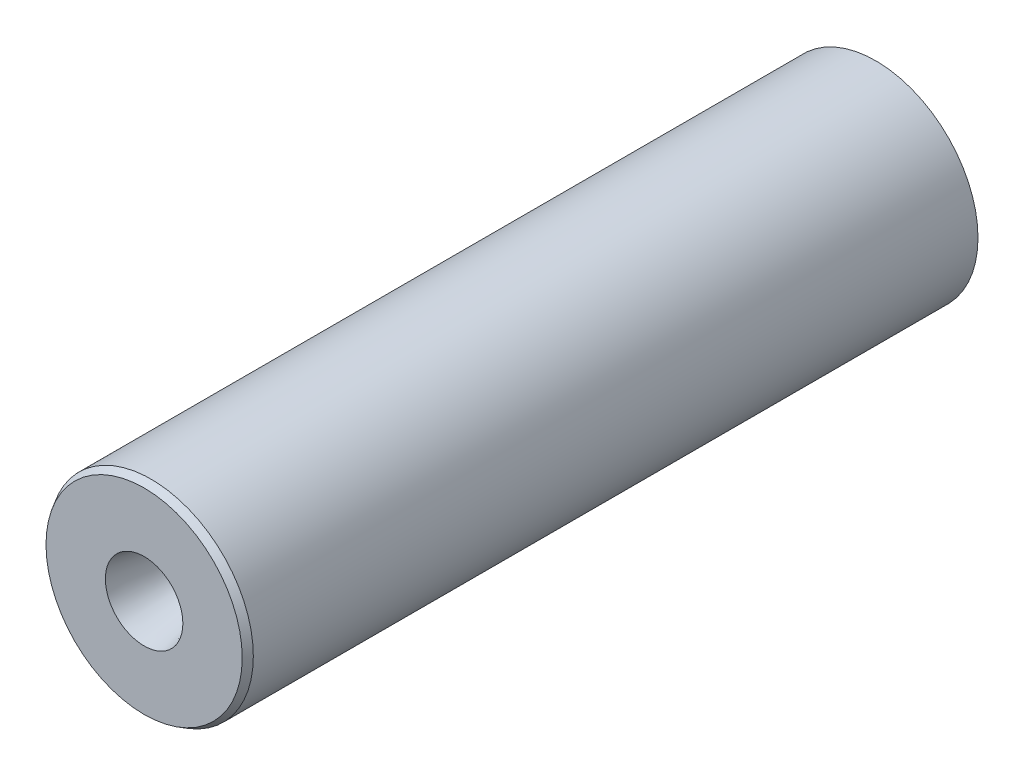
SolidWorks part; units mm, degrees
material "PLA"
ref_plane "Plan de face" through (0, 0, 0) normal (0, 0, 1) x (1, 0, 0)
ref_plane "Plan de dessus" through (0, 0, 0) normal (0, 1, 0) x (1, 0, 0)
ref_plane "Plan de droite" through (0, 0, 0) normal (1, 0, 0) x (0, 0, -1)
sketch "Esquisse1" plane through (0, 0, 0) normal (1, 0, 0) x (0, 0, -1)
  line L0 (-51.9182, 0) -> (51.9182, 0) construction
  line L1 (36.9182, 11) -> (36.9182, 9)
  line L2 (-51.9182, 14.5) -> (51.9182, 14.5)
  line L4 (-23.0818, 11) -> (36.9182, 11)
  line L6 (36.9182, 9) -> (51.9182, 9)
  line L7 (51.9182, 14.5) -> (51.9182, 9)
  line L8 (-23.0818, 11) -> (-37.8043, 2.5)
  line L9 (-37.8043, 2.5) -> (-51.9182, 5.5)
  line L10 (-51.9182, 14.5) -> (-51.9182, 5.5)
  line L11 (-47.6261, 7.6547) -> (-41.6462, 6.3836) construction
  line L12 (-47.4182, 11.5) -> (-33.9479, 11.5) construction
  line L13 (-48.4182, 10.5) -> (-48.4182, 8.6329) construction
  line L16 (-38.1066, 6.9443) -> (-33.4479, 9.634) construction
  arc A0 (-33.9479, 11.5) -> (-33.4479, 9.634) centre (-33.9479, 10.5) cw construction
  arc A1 (-48.4182, 8.6329) -> (-47.6261, 7.6547) centre (-47.4182, 8.6329) ccw construction
  arc A2 (-47.4182, 11.5) -> (-48.4182, 10.5) centre (-47.4182, 10.5) ccw construction
  arc A3 (-41.6462, 6.3836) -> (-38.1066, 6.9443) centre (-40.6066, 11.2744) ccw construction
  dimension "D14" = 1
  dimension "D15" = 5
  dimension "D1" = 60
  dimension "D2" = 11
  dimension "D3" = 14.5
  dimension "D4" = 15
  dimension "D5" = 9
  dimension "D6" = 2.5
  dimension "D7" = 30
  dimension "D8" = 12
  dimension "D9" = 5.5
  dimension "D10" = 3.5
  dimension "D11" = 3
  dimension "D12" = 3
  dimension "D13" = 4
revolve "Révolution1" add sketch "Esquisse1" angle 360 about L0
ref_plane "Plan de face-Bouchon" through (0, 0, -48.4182) normal (0, 0, -1) x (1, 0, 0)
ref_plane "Plan de dessus-Bouchon" through (0, 0, -48.4182) normal (0, -1, 0) x (1, 0, 0)
ref_plane "Plan de droite-Bouchon" through (0, 0, -48.4182) normal (1, 0, 0) x (0, 0, 1)
inserted part "Bouchon"
move or copy body "Corps-Déplacer/Copier2"
other "Embouti1" [suppressed] parameters "D1"=10, "D2"=0.2
sketch "Esquisse2" plane through (0, 0, -51.9182) normal (0, 0, -1) x (-1, 0, 0)
  circle A0 centre (0, 0) radius 11
  circle A1 centre (0, 0) radius 11 construction
extrude "Enlèv. mat.-Extru.1" cut sketch "Esquisse2" against normal up to surface (15 mm away) up to face at (9, 0, -36.9182)
sketch "Esquisse3" plane through (0, 0, 0) normal (1, 0, 0) x (0, 0, -1)
  line L0 (48.9182, 11) -> (48.9182, 12)
  line L1 (51.9182, 11) -> (-23.0818, 11) construction
  line L2 (48.9182, 12) -> (46.9182, 12)
  line L3 (46.9182, 12) -> (46.9182, 11)
  line L4 (46.9182, 11) -> (43.9182, 11)
  line L5 (43.9182, 11) -> (43.9182, 12)
  line L6 (43.9182, 12) -> (41.9182, 12)
  line L7 (41.9182, 12) -> (41.9182, 11)
  line L8 (41.9182, 11) -> (38.9182, 11)
  line L9 (38.9182, 11) -> (38.9182, 12)
  line L10 (38.9182, 12) -> (36.9182, 12)
  line L11 (36.9182, 12) -> (36.9182, 11)
  line L12 (48.9182, 11) -> (51.9182, 11)
  line L13 (51.9182, -14.5) -> (51.9182, 14.5) construction
  line L14 (0, 0) -> (51.9182, 0) construction
  line L15 (36.9182, 11) -> (36.9182, 0)
  line L16 (51.9182, 11) -> (51.9182, 0)
  line L17 (51.9182, 0) -> (36.9182, 0)
  line L18 (-23.0818, 11) -> (-23.0818, -11) construction
  dimension "D1" = 60
  dimension "D2" = 2
  dimension "D3" = 1
revolve "Enlèvement de matière-Révolution1" cut sketch "Esquisse3" angle 360 about L14
fillet "Congé1" radius 5 2 edges at (2.5, 0, 37.8043) (11, 0, 23.0818)
chamfer "Chanfrein1" distance 1 angle 30 1 edges at (14.5, 0, 51.9182)
